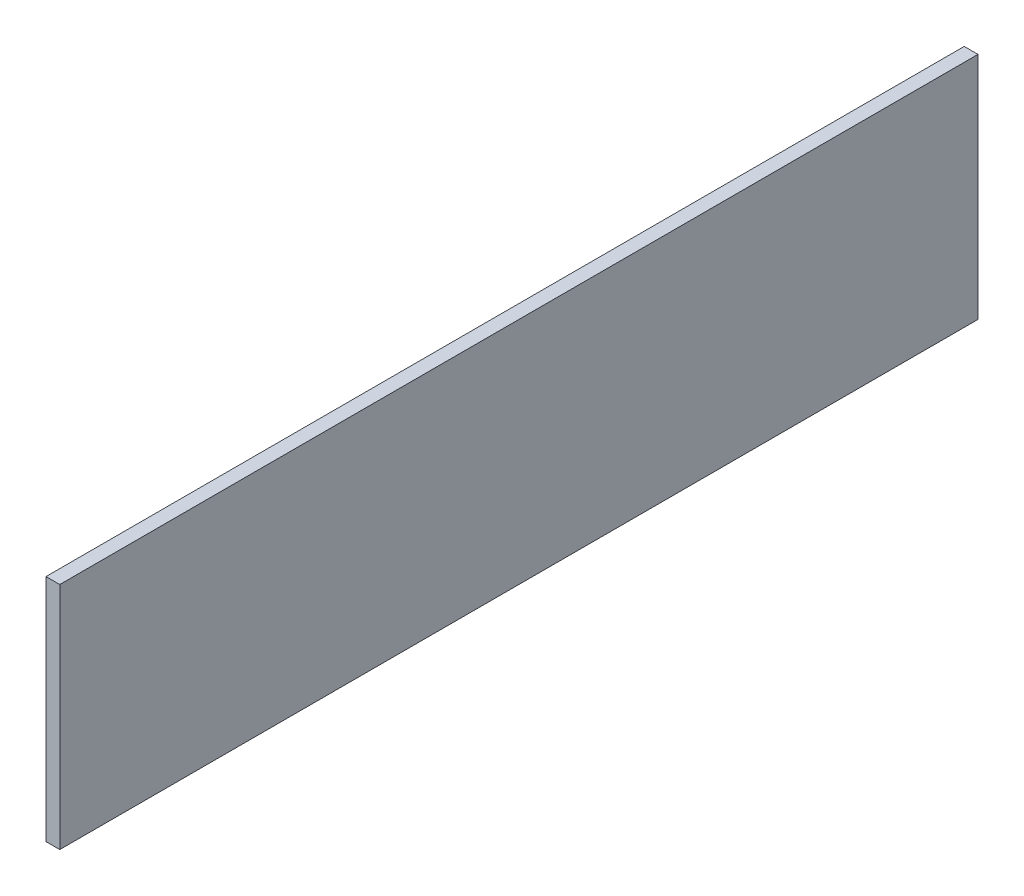
SolidWorks part; units mm, degrees
ref_plane "Front Plane" through (0, 0, 0) normal (0, 0, 1) x (1, 0, 0)
ref_plane "Top Plane" through (0, 0, 0) normal (0, 1, 0) x (1, 0, 0)
ref_plane "Right Plane" through (0, 0, 0) normal (1, 0, 0) x (0, 0, -1)
sketch "Sketch1" plane through (0, 0, 0) normal (1, 0, 0) x (0, 0, -1)
  line L0 (100, -31) -> (-100, -31) construction
  line L1 (-100, 25) -> (100, 25)
  line L2 (-100, 25) -> (-100, -25)
  line L3 (-100, -25) -> (100, -25)
  line L4 (100, 25) -> (100, -25)
  point P4 (0, -25)
  point P6 (-100, 0)
  dimension "D2" = 50
extrude "Boss-Extrude1" add sketch "Sketch1" along normal blind 3
